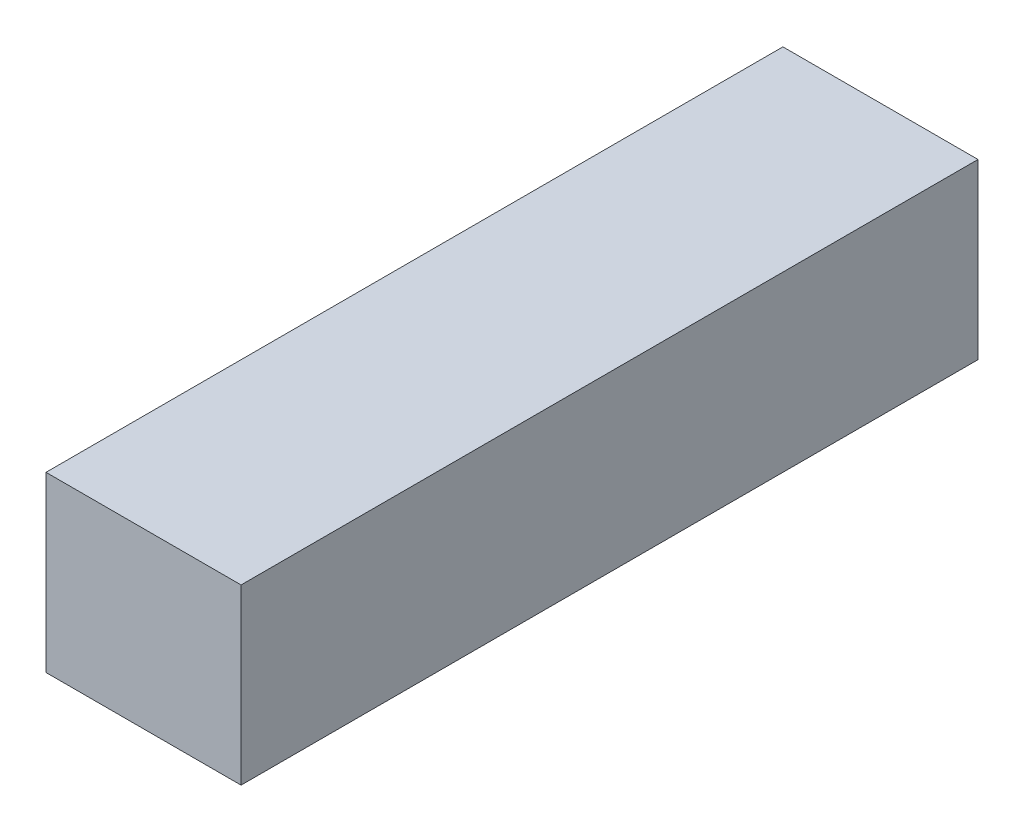
SolidWorks part; units mm, degrees
ref_plane "Plan de face" through (0, 0, 0) normal (0, 0, 1) x (1, 0, 0)
ref_plane "Plan de dessus" through (0, 0, 0) normal (0, 1, 0) x (1, 0, 0)
ref_plane "Plan de droite" through (0, 0, 0) normal (1, 0, 0) x (0, 0, -1)
sketch "Esquisse1" plane through (0, 0, 0) normal (0, 0, 1) x (1, 0, 0)
  line L1 (-36.1156, 22.4038) -> (8.8844, 22.4038)
  line L2 (-36.1156, 22.4038) -> (-36.1156, -17.5962)
  line L3 (-36.1156, -17.5962) -> (8.8844, -17.5962)
  line L4 (8.8844, 22.4038) -> (8.8844, -17.5962)
  dimension "D1" = 40
  dimension "D2" = 45
extrude "Boss.-Extru.1" add sketch "Esquisse1" along normal blind 170
